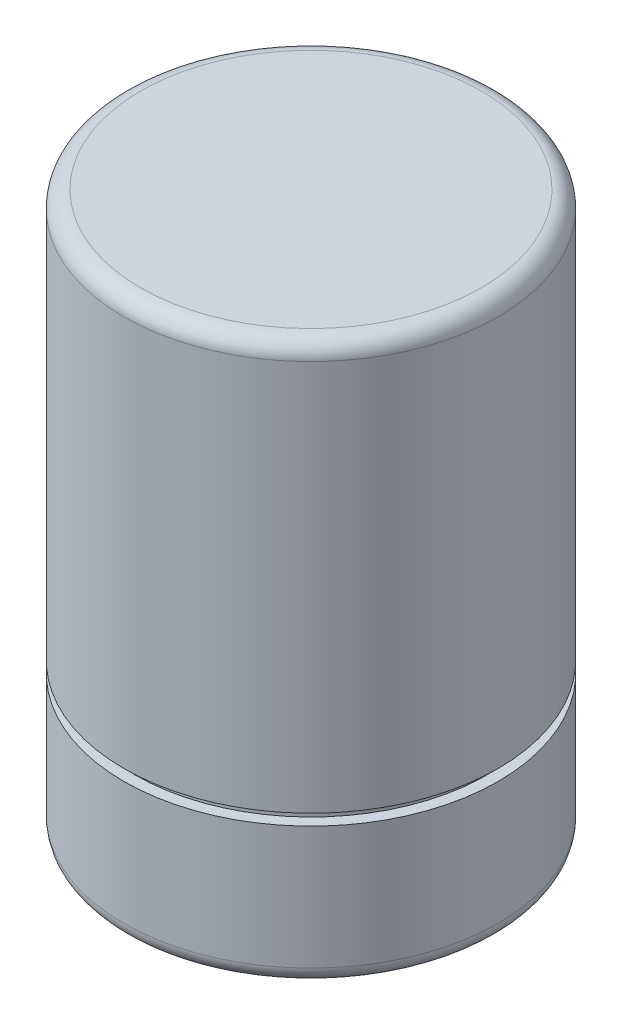
SolidWorks part; units mm, degrees
ref_plane "Front Plane" through (0, 0, 0) normal (0, 0, 1) x (1, 0, 0)
ref_plane "Top Plane" through (0, 0, 0) normal (0, 1, 0) x (1, 0, 0)
ref_plane "Right Plane" through (0, 0, 0) normal (1, 0, 0) x (0, 0, -1)
sketch "Sketch2" plane through (0, 0, 0) normal (1, 0, 0) x (0, 0, -1)
  line L0 (0, 0) -> (0, 100)
  line L1 (0, 100) -> (33.5, 100)
  line L2 (33.5, 100) -> (33.5, 27)
  line L3 (33.5, 27) -> (31.5, 27)
  line L4 (31.5, 27) -> (31.5, 25)
  line L5 (31.5, 25) -> (33.5, 25)
  line L6 (33.5, 25) -> (33.5, 0)
  line L7 (33.5, 0) -> (0, 0)
  dimension "D1" = 100
  dimension "D2" = 33.5
  dimension "D3" = 33.5
  dimension "D4" = 25
  dimension "D5" = 73
  dimension "D6" = 2
revolve "Revolve1" add sketch "Sketch2" angle 360 about L0
fillet "Fillet1" radius 3 1 edges at (0, 100, -33.5)
fillet "Fillet2" radius 3 1 edges at (0, 0, -33.5)
